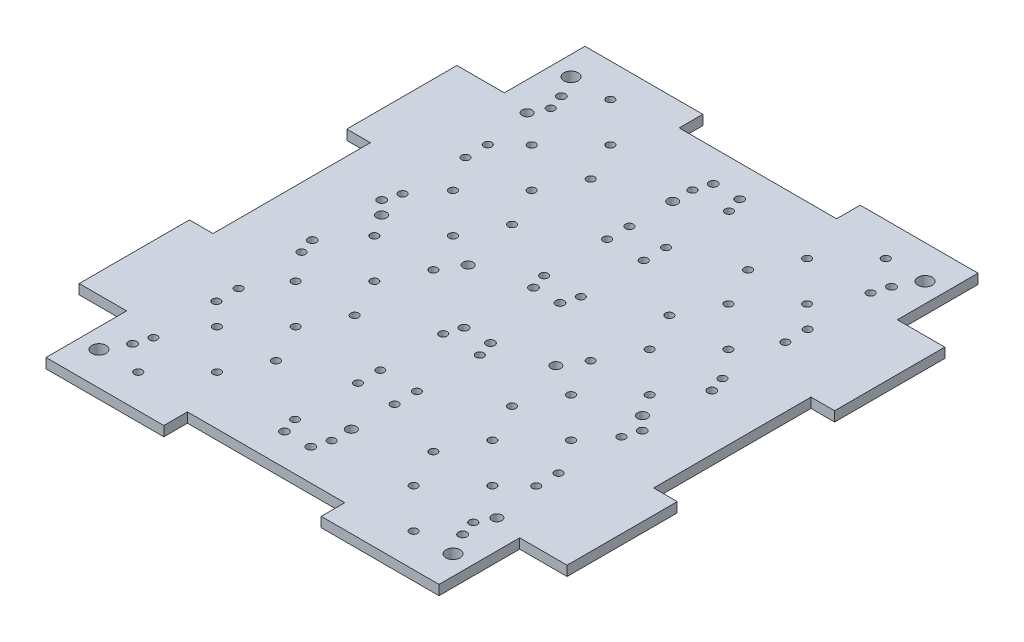
SolidWorks part; units mm, degrees
ref_plane "Front Plane" through (0, 0, 0) normal (0, 0, 1) x (1, 0, 0)
ref_plane "Top Plane" through (0, 0, 0) normal (0, 1, 0) x (1, 0, 0)
ref_plane "Right Plane" through (0, 0, 0) normal (1, 0, 0) x (0, 0, -1)
sketch "Sketch1" plane through (0, 0, 0) normal (0, 1, 0) x (1, 0, 0)
  line L0 (-25.4, 86.995) -> (-63.4314, 86.995)
  line L1 (-88.9, -101.6) -> (88.9, -101.6) construction
  line L2 (101.6, -88.9) -> (101.6, 88.9) construction
  line L3 (88.9, 101.6) -> (-88.9, 101.6) construction
  line L4 (-78.74, -60.96) -> (-63.4314, -60.96)
  line L5 (-63.4314, -60.96) -> (-63.4314, -86.995)
  line L6 (-63.4314, -86.995) -> (-25.4, -86.995)
  line L7 (63.4314, -86.995) -> (63.4314, -60.96)
  line L8 (63.4314, -60.96) -> (78.74, -60.96)
  line L9 (78.74, -60.96) -> (78.74, -25.4)
  line L10 (78.74, 60.96) -> (63.4314, 60.96)
  line L11 (63.4314, 60.96) -> (63.4314, 86.995)
  line L12 (63.4314, 86.995) -> (25.4, 86.995)
  line L13 (-63.4314, 86.995) -> (-63.4314, 60.96)
  line L14 (-63.4314, 60.96) -> (-78.74, 60.96)
  line L15 (-78.74, 60.96) -> (-78.74, 25.4)
  line L16 (-78.74, -25.4) -> (-78.74, -60.96)
  line L17 (-78.74, -25.4) -> (-71.12, -25.4)
  line L19 (-78.74, 25.4) -> (-71.12, 25.4)
  line L20 (-71.12, -25.4) -> (-71.12, 25.4)
  line L22 (-25.4, 86.995) -> (-25.4, 79.375)
  line L23 (-25.4, 79.375) -> (25.4, 79.375)
  line L24 (25.4, 86.995) -> (25.4, 79.375)
  line L25 (78.74, 25.4) -> (71.12, 25.4)
  line L27 (78.74, -25.4) -> (71.12, -25.4)
  line L28 (71.12, 25.4) -> (71.12, -25.4)
  line L30 (25.4, -86.995) -> (25.4, -79.375)
  line L31 (25.4, -79.375) -> (-25.4, -79.375)
  line L32 (-25.4, -86.995) -> (-25.4, -79.375)
  line L33 (78.74, 25.4) -> (78.74, 60.96)
  line L34 (25.4, -86.995) -> (63.4314, -86.995)
  line L35 (-101.6, 88.9) -> (-101.6, -88.9) construction
  arc A0 (88.9, -101.6) -> (101.6, -88.9) centre (88.9, -88.9) ccw construction
  arc A1 (-101.6, -88.9) -> (-88.9, -101.6) centre (-88.9, -88.9) ccw construction
  arc A2 (101.6, 88.9) -> (88.9, 101.6) centre (88.9, 88.9) ccw construction
  arc A3 (-101.6, 88.9) -> (-88.9, 101.6) centre (-88.9, 88.9) cw construction
  circle A4 centre (-57.15, 76.2) radius 2.286
  circle A5 centre (57.15, 76.2) radius 2.286
  circle A6 centre (57.15, -76.2) radius 2.286
  circle A7 centre (-57.15, -76.2) radius 2.286
  point P3 (0, 101.6)
  point P5 (101.6, 0)
  point P13 (101.6, 101.6)
  point P16 (-101.6, 101.6)
  point P38 (-71.12, 0)
  point P55 (0, -79.375)
  point P56 (0, 79.375)
  point P57 (71.12, 0)
  dimension "D2" = 12.7
  dimension "D11" = 4.572
  dimension "D8" = 44.45
  dimension "D1" = 203.2
  dimension "D3" = 203.2
  dimension "D4" = 22.86
  dimension "D5" = 15.3086
  dimension "D6" = 35.56
  dimension "D7" = 173.99
  dimension "D12" = 50.8
  dimension "D13" = 25.4
  dimension "D14" = 44.45
  dimension "D15" = 25.4
  dimension "D18" = 7.62
extrude "Boss-Extrude1" add sketch "Sketch1" along normal blind 3.175
sketch "Sketch2" plane through (0, 3.175, 0) normal (0, 1, 0) x (1, 0, 0)
  line L0 (-25.4, -79.375) -> (25.4, -79.375) construction
  line L2 (-63.4314, -60.96) -> (-63.4314, -86.995) construction
  line L3 (0, 0) -> (0, 50000) construction
  line L4 (-1000, 0) -> (49000, 0) construction
  circle A0 centre (-53.2714, -69.215) radius 1.35
  circle A1 centre (-4.2714, -69.215) radius 1.35
  circle A2 centre (-4.2714, -11.215) radius 1.35
  circle A3 centre (-53.2714, -11.215) radius 1.35
  circle A4 centre (53.2714, -11.215) radius 1.35
  circle A5 centre (4.2714, -11.215) radius 1.35
  circle A6 centre (4.2714, -69.215) radius 1.35
  circle A7 centre (53.2714, -69.215) radius 1.35
  circle A8 centre (53.2714, 11.215) radius 1.35
  circle A9 centre (53.2714, 69.215) radius 1.35
  circle A10 centre (4.2714, 69.215) radius 1.35
  circle A11 centre (4.2714, 11.215) radius 1.35
  circle A12 centre (-4.2714, 11.215) radius 1.35
  circle A13 centre (-4.2714, 69.215) radius 1.35
  circle A14 centre (-53.2714, 11.215) radius 1.35
  circle A15 centre (-53.2714, 69.215) radius 1.35
  dimension "D1" = 2.7
  dimension "D2" = 58
  dimension "D3" = 49
  dimension "D4" = 10.16
  dimension "D5" = 10.16
extrude "Raspberry Pi Holes" cut sketch "Sketch2" against normal through all
sketch "Sketch3" plane through (0, 3.175, 0) normal (0, 1, 0) x (1, 0, 0)
  line L0 (-53.2714, -11.215) -> (-4.2714, -11.215) construction
  line L1 (-51.6314, -43.815) -> (-5.9114, -43.815) construction
  line L2 (-1000, 0) -> (49000, 0) construction
  line L3 (0, -1000) -> (0, 49000) construction
  line L4 (51.6314, -43.815) -> (5.9114, -43.815) construction
  line L5 (53.2714, -11.215) -> (4.2714, -11.215) construction
  line L6 (53.2714, 11.215) -> (4.2714, 11.215) construction
  line L7 (51.6314, 43.815) -> (5.9114, 43.815) construction
  line L8 (-51.6314, 43.815) -> (-5.9114, 43.815) construction
  line L9 (-53.2714, 11.215) -> (-4.2714, 11.215) construction
  circle A0 centre (-51.6314, -64.135) radius 1.27
  circle A1 centre (-5.9114, -64.135) radius 1.27
  circle A2 centre (-5.9114, -43.815) radius 1.27
  circle A3 centre (-51.6314, -43.815) radius 1.27
  circle A4 centre (-53.2714, -69.215) radius 1.35 construction
  circle A5 centre (-51.6314, -16.295) radius 1.27
  circle A6 centre (-51.6314, -36.615) radius 1.27
  circle A7 centre (-5.9114, -36.615) radius 1.27
  circle A8 centre (-5.9114, -16.295) radius 1.27
  circle A9 centre (-53.2714, -11.215) radius 1.35 construction
  circle A10 centre (5.9114, -16.295) radius 1.27
  circle A11 centre (5.9114, -36.615) radius 1.27
  circle A12 centre (51.6314, -36.615) radius 1.27
  circle A13 centre (51.6314, -16.295) radius 1.27
  circle A14 centre (51.6314, -43.815) radius 1.27
  circle A15 centre (5.9114, -43.815) radius 1.27
  circle A16 centre (5.9114, -64.135) radius 1.27
  circle A17 centre (51.6314, -64.135) radius 1.27
  circle A18 centre (51.6314, 64.135) radius 1.27
  circle A19 centre (5.9114, 64.135) radius 1.27
  circle A20 centre (5.9114, 43.815) radius 1.27
  circle A21 centre (51.6314, 43.815) radius 1.27
  circle A22 centre (51.6314, 16.295) radius 1.27
  circle A23 centre (51.6314, 36.615) radius 1.27
  circle A24 centre (5.9114, 36.615) radius 1.27
  circle A25 centre (5.9114, 16.295) radius 1.27
  circle A26 centre (-5.9114, 16.295) radius 1.27
  circle A27 centre (-5.9114, 36.615) radius 1.27
  circle A28 centre (-51.6314, 36.615) radius 1.27
  circle A29 centre (-51.6314, 16.295) radius 1.27
  circle A30 centre (-51.6314, 43.815) radius 1.27
  circle A31 centre (-5.9114, 43.815) radius 1.27
  circle A32 centre (-5.9114, 64.135) radius 1.27
  circle A33 centre (-51.6314, 64.135) radius 1.27
  point P8 (-28.7714, -43.815)
  point P9 (-28.7714, -11.215)
  dimension "D1" = 2.54
  dimension "D2" = 45.72
  dimension "D3" = 20.32
  dimension "D4" = 5.08
  dimension "D6" = 5.08
  dimension "D5" = 2
extrude "Feather Board Holes" cut sketch "Sketch3" against normal through all
sketch "Sketch4" plane through (0, 3.175, 0) normal (0, 1, 0) x (1, 0, 0)
  circle A3 centre (5.9114, -57.785) radius 1.6
  circle A4 centre (21.1514, -6.985) radius 1.6
  circle A5 centre (49.0914, -6.985) radius 1.6
  circle A6 centre (54.1714, -59.055) radius 1.6
  circle A8 centre (5.9114, -64.135) radius 1.27 construction
  point P15 (5.9114, -64.135)
  dimension "D4" = 5.08
  dimension "D5" = 3.2
  dimension "D6" = 6.35
  dimension "D7" = 1.27
  dimension "D1" = 50.8
  dimension "D2" = 27.94
  dimension "D3" = 15.24
extrude "Arduino Uno 1" cut sketch "Sketch4" against normal through all
sketch "Sketch5" plane through (0, 3.175, 0) normal (0, 1, 0) x (1, 0, 0)
  circle A0 centre (-5.9114, 57.785) radius 1.6
  circle A1 centre (-54.1714, 59.055) radius 1.6
  circle A2 centre (-49.0914, 6.985) radius 1.6
  circle A3 centre (-21.1514, 6.985) radius 1.6
  circle A5 centre (-5.9114, 64.135) radius 1.27 construction
  point P9 (-5.9114, 64.135)
  dimension "D1" = 3.2
  dimension "D2" = 50.8
  dimension "D3" = 15.24
  dimension "D4" = 27.94
  dimension "D5" = 5.08
  dimension "D6" = 6.35
  dimension "D7" = 1.27
extrude "Arduino Uno 2" cut sketch "Sketch5" against normal through all
sketch "Sketch6" plane through (0, 3.175, 0) normal (0, 1, 0) x (1, 0, 0)
  line L0 (44.45, 76.2) -> (-44.45, 76.2) construction
  line L1 (25.4, 79.375) -> (-25.4, 79.375) construction
  line L4 (44.45, 76.2) -> (44.4157, 86.995) construction
  line L6 (63.4314, 86.995) -> (25.4, 86.995) construction
  line L8 (44.45, -76.2) -> (44.4157, -86.995) construction
  line L9 (25.4, -86.995) -> (63.4314, -86.995) construction
  circle A0 centre (44.45, 76.2) radius 1.27
  circle A1 centre (-44.45, 76.2) radius 1.27
  circle A3 centre (44.45, 50.8) radius 1.27
  circle A4 centre (-44.45, 50.8) radius 1.27
  circle A5 centre (44.45, 25.4) radius 1.27
  circle A6 centre (-44.45, 25.4) radius 1.27
  circle A7 centre (44.45, 0) radius 1.27
  circle A8 centre (-44.45, 0) radius 1.27
  circle A9 centre (44.45, -25.4) radius 1.27
  circle A10 centre (-44.45, -25.4) radius 1.27
  circle A11 centre (44.45, -50.8) radius 1.27
  circle A12 centre (-44.45, -50.8) radius 1.27
  circle A13 centre (44.45, -76.2) radius 1.27
  circle A14 centre (-44.45, -76.2) radius 1.27
  point P4 (0, 76.2)
  point P7 (0, 79.375)
  dimension "D1" = 2.54
  dimension "D2" = 88.9
  dimension "D4" = 25.4
  dimension "D3" = 7
extrude "Custom PCB 3 inch" cut sketch "Sketch6" against normal through all
sketch "Sketch7" plane through (0, 3.175, 0) normal (0, 1, 0) x (1, 0, 0)
  line L0 (-31.75, -63.5) -> (31.75, -63.5) construction
  line L5 (-25.4, -79.375) -> (25.4, -79.375) construction
  line L6 (-31.75, 63.5) -> (31.75, 63.5) construction
  line L7 (0, 63.5) -> (0, 79.375) construction
  line L8 (25.4, 79.375) -> (-25.4, 79.375) construction
  line L9 (0, -63.5) -> (0, -79.375) construction
  circle A0 centre (-31.75, -63.5) radius 1.27
  circle A1 centre (31.75, -63.5) radius 1.27
  circle A2 centre (31.75, -38.1) radius 1.27
  circle A3 centre (-31.75, -38.1) radius 1.27
  circle A4 centre (31.75, -12.7) radius 1.27
  circle A5 centre (-31.75, -12.7) radius 1.27
  circle A6 centre (31.75, 12.7) radius 1.27
  circle A7 centre (-31.75, 12.7) radius 1.27
  circle A8 centre (31.75, 38.1) radius 1.27
  circle A9 centre (-31.75, 38.1) radius 1.27
  circle A10 centre (31.75, 63.5) radius 1.27
  circle A11 centre (-31.75, 63.5) radius 1.27
  point P4 (0, -63.5)
  point P7 (0, -79.375)
  dimension "D1" = 2.54
  dimension "D2" = 63.5
  dimension "D3" = 6
  dimension "D4" = 25.4
extrude "Custom PCB 2.5 inch" cut sketch "Sketch7" against normal through all
sketch "Sketch8" plane through (0, 3.175, 0) normal (0, 1, 0) x (1, 0, 0)
  line L0 (-25.4, -50.8) -> (25.4, -50.8) construction
  line L1 (-25.4, -79.375) -> (25.4, -79.375) construction
  line L2 (-25.4, -25.4) -> (25.4, -25.4) construction
  line L3 (-25.4, 0) -> (25.4, 0) construction
  line L4 (-25.4, 25.4) -> (25.4, 25.4) construction
  line L5 (-25.4, 50.8) -> (25.4, 50.8) construction
  line L6 (0, 50.8) -> (0, 79.375) construction
  line L7 (25.4, 79.375) -> (-25.4, 79.375) construction
  line L8 (0, -50.8) -> (0, -79.375) construction
  circle A0 centre (-25.4, -50.8) radius 1.27
  circle A1 centre (25.4, -50.8) radius 1.27
  circle A2 centre (-25.4, -25.4) radius 1.27
  circle A3 centre (25.4, -25.4) radius 1.27
  circle A4 centre (-25.4, 0) radius 1.27
  circle A5 centre (25.4, 0) radius 1.27
  circle A6 centre (-25.4, 25.4) radius 1.27
  circle A7 centre (25.4, 25.4) radius 1.27
  circle A8 centre (-25.4, 50.8) radius 1.27
  circle A9 centre (25.4, 50.8) radius 1.27
  point P4 (0, -50.8)
  point P7 (0, -79.375)
  dimension "D1" = 50.8
  dimension "D2" = 2.54
  dimension "D4" = 25.4
  dimension "D3" = 5
extrude "Custom PCB 2 inch" cut sketch "Sketch8" against normal through all
